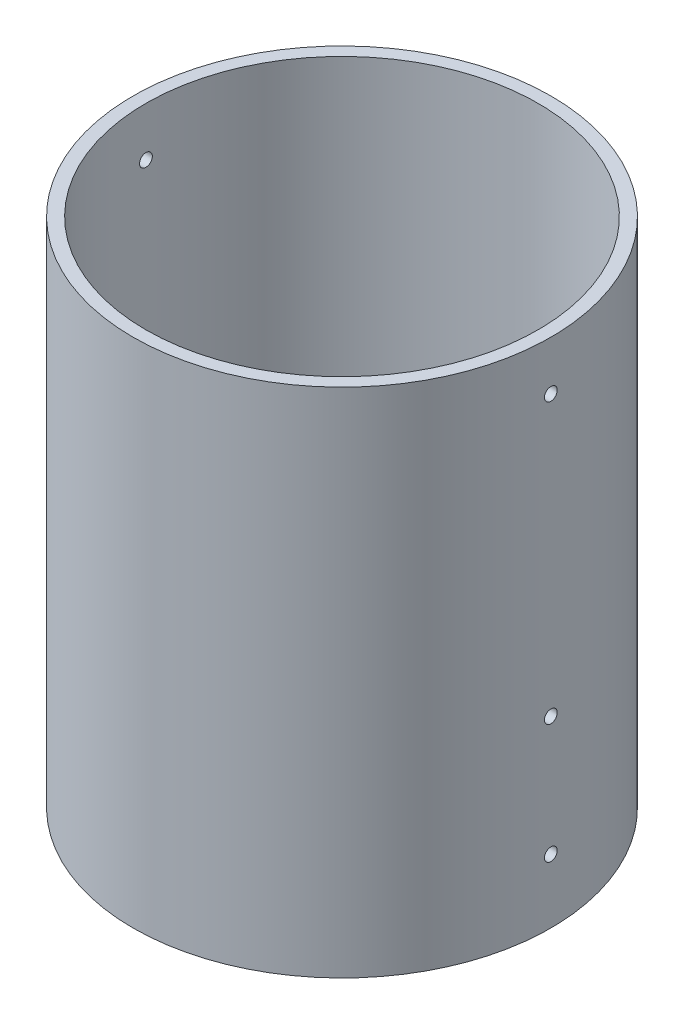
SolidWorks part; units mm, degrees
ref_plane "Front Plane" through (0, 0, 0) normal (0, 0, 1) x (1, 0, 0)
ref_plane "Top Plane" through (0, 0, 0) normal (0, 1, 0) x (1, 0, 0)
ref_plane "Right Plane" through (0, 0, 0) normal (1, 0, 0) x (0, 0, -1)
sketch "Sketch2" plane through (0, 0, 0) normal (0, 1, 0) x (1, 0, 0)
  circle A0 centre (0, 0) radius 46
  circle A1 centre (0, 0) radius 49
  dimension "D1" = 92
  dimension "D2" = 98
extrude "Boss-Extrude1" add sketch "Sketch2" along normal blind 120
sketch "Sketch5" plane through (0, 0, 0) normal (1, 0, 0) x (0, 0, -1)
  line L0 (0, 0) -> (0, 108.5) construction
  circle A0 centre (0, 108.5) radius 1.5
  dimension "D2" = 3
  dimension "D1" = 108.5
extrude "Cut-Extrude2" cut sketch "Sketch5" against normal through all and the other way through all
sketch "Sketch6" plane through (0, 0, 0) normal (1, 0, 0) x (0, 0, -1)
  line L0 (0, 0) -> (0, 15) construction
  line L2 (0, 29) -> (21.0526, 29) construction
  circle A0 centre (0, 15) radius 1.5
  circle A1 centre (0, 43) radius 1.5
  dimension "D3" = 3
  dimension "D1" = 15
  dimension "D2" = 14
extrude "Cut-Extrude3" cut sketch "Sketch6" against normal through all and the other way through all
